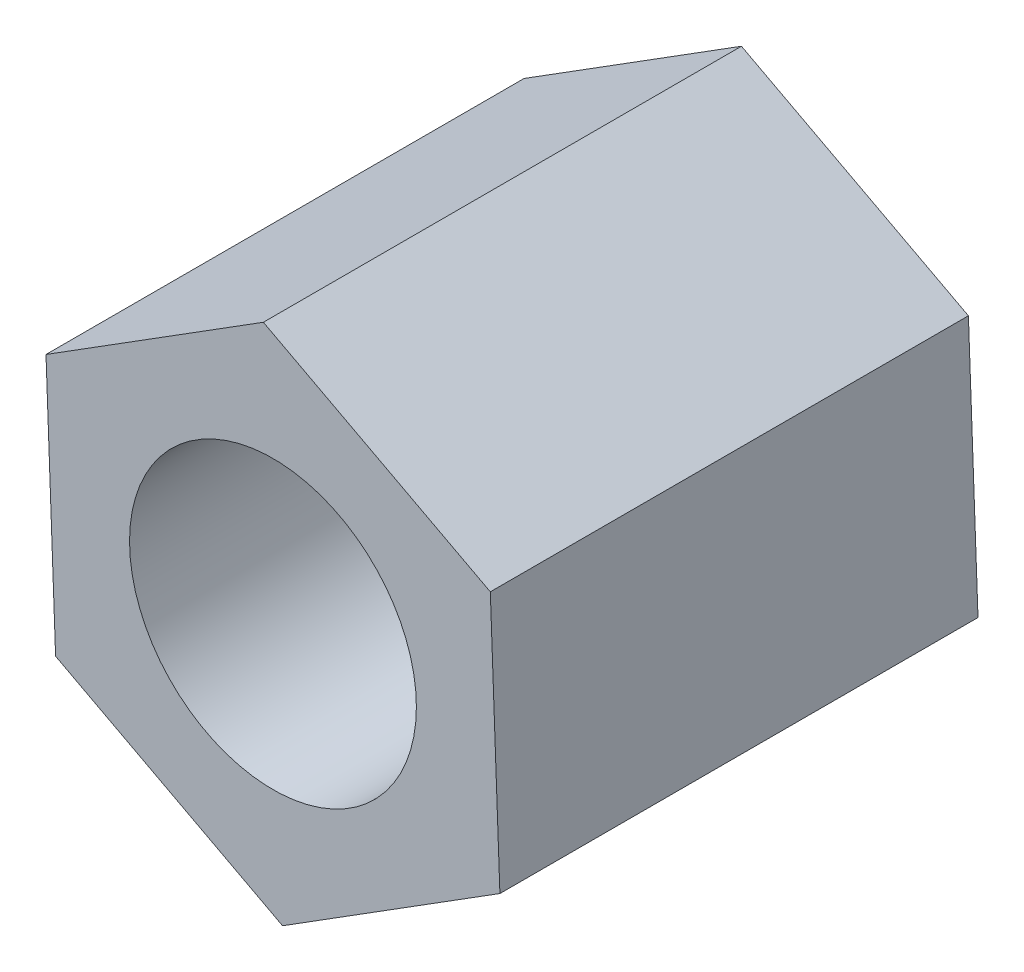
SolidWorks part; units mm, degrees
ref_plane "前视基准面" through (0, 0, 0) normal (0, 0, 1) x (1, 0, 0)
ref_plane "上视基准面" through (0, 0, 0) normal (0, 1, 0) x (1, 0, 0)
ref_plane "右视基准面" through (0, 0, 0) normal (1, 0, 0) x (0, 0, -1)
sketch "草图1" plane through (0, 0, 0) normal (0, 0, 1) x (1, 0, 0)
  line L1 (2.2732, 1.4283) -> (-0.1003, 2.6828)
  line L2 (-0.1003, 2.6828) -> (-2.3735, 1.2545)
  line L3 (-2.3735, 1.2545) -> (-2.2732, -1.4283)
  line L4 (-2.2732, -1.4283) -> (0.1003, -2.6828)
  line L5 (0.1003, -2.6828) -> (2.3735, -1.2545)
  line L6 (2.3735, -1.2545) -> (2.2732, 1.4283)
  circle A0 centre (0, 0) radius 2.325 construction
  circle A1 centre (0, 0) radius 1.5
extrude "凸台-拉伸1" add sketch "草图1" along normal blind 5
